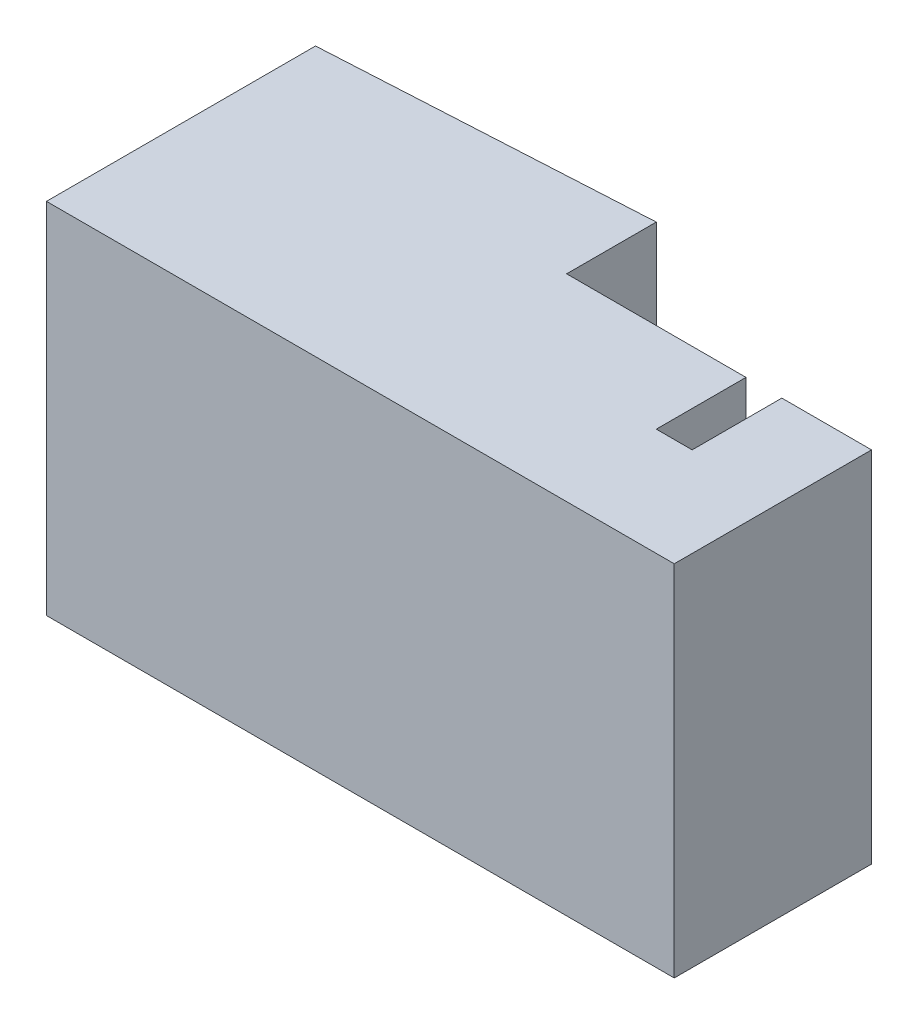
SolidWorks part; units mm, degrees
ref_plane "Front Plane" through (0, 0, 0) normal (0, 0, 1) x (1, 0, 0)
ref_plane "Top Plane" through (0, 0, 0) normal (0, 1, 0) x (1, 0, 0)
ref_plane "Right Plane" through (0, 0, 0) normal (1, 0, 0) x (0, 0, -1)
sketch "Sketch1" plane through (0, 0, 0) normal (0, 1, 0) x (1, 0, 0)
  line L0 (0, 0) -> (35, 0)
  line L1 (0, 0) -> (0, 15)
  line L2 (18, 16) -> (18, 11)
  line L3 (35, 11) -> (35, 0)
  line L4 (18, 11) -> (28, 11)
  line L5 (18, 16) -> (0, 15)
  line L6 (28, 11) -> (28, 6)
  line L7 (28, 6) -> (30, 6)
  line L8 (30, 6) -> (30, 11)
  line L9 (30, 11) -> (35, 11)
extrude "Boss-Extrude1" add sketch "Sketch1" along normal blind 20
